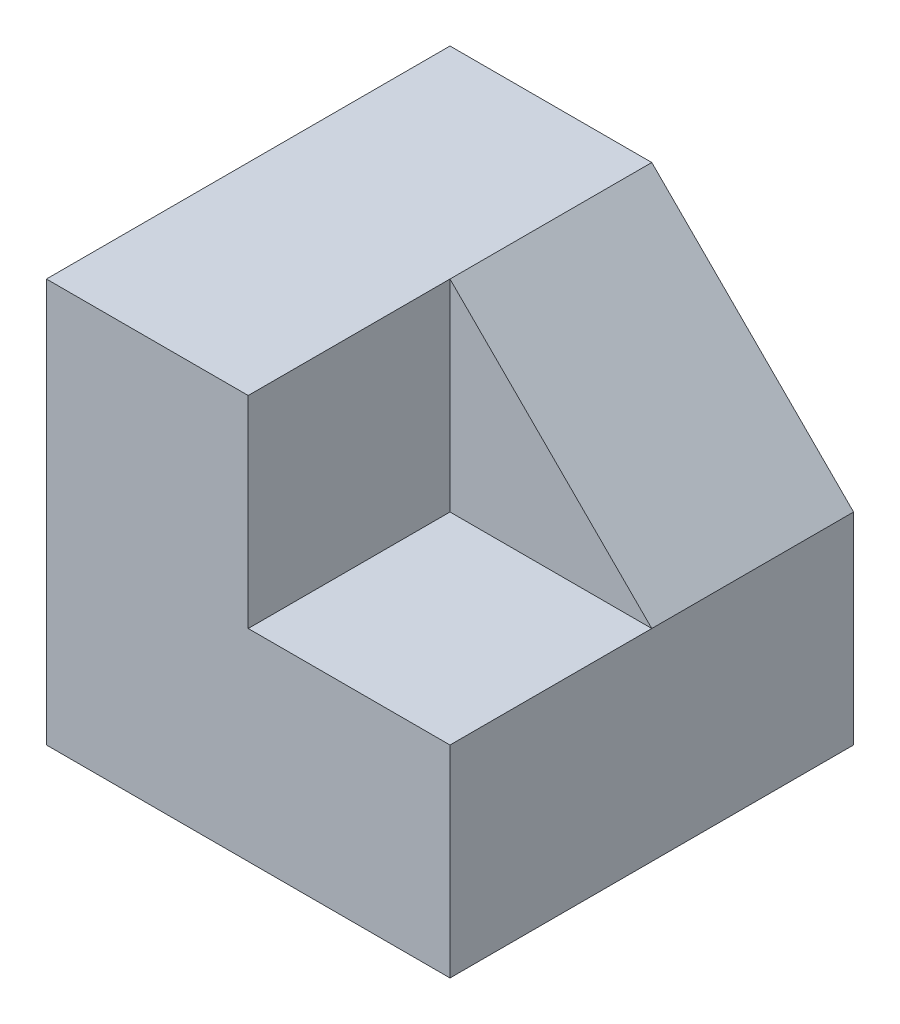
SolidWorks part; units mm, degrees
ref_plane "Alzado" through (0, 0, 0) normal (0, 0, 1) x (1, 0, 0)
ref_plane "Planta" through (0, 0, 0) normal (0, 1, 0) x (1, 0, 0)
ref_plane "Vista lateral" through (0, 0, 0) normal (1, 0, 0) x (0, 0, -1)
sketch "Croquis1" plane through (0, 0, 0) normal (0, 0, 1) x (1, 0, 0)
  line L0 (0, 0) -> (0, 60)
  line L3 (60, 0) -> (0, 0)
  line L4 (0, 60) -> (30, 60)
  line L5 (30, 60) -> (60, 30)
  line L6 (60, 30) -> (60, 0)
  dimension "D1" = 60
  dimension "D2" = 30
extrude "Saliente-Extruir1" add sketch "Croquis1" against normal blind 60
sketch "Croquis2" plane through (0, 0, 0) normal (0, 0, 1) x (1, 0, 0)
  line L0 (60, 30) -> (30, 60) construction
  line L1 (60, 30) -> (30, 60)
  line L2 (30, 60) -> (30, 30)
  line L3 (30, 30) -> (60, 30)
extrude "Cortar-Extruir1" cut sketch "Croquis2" against normal blind 30
